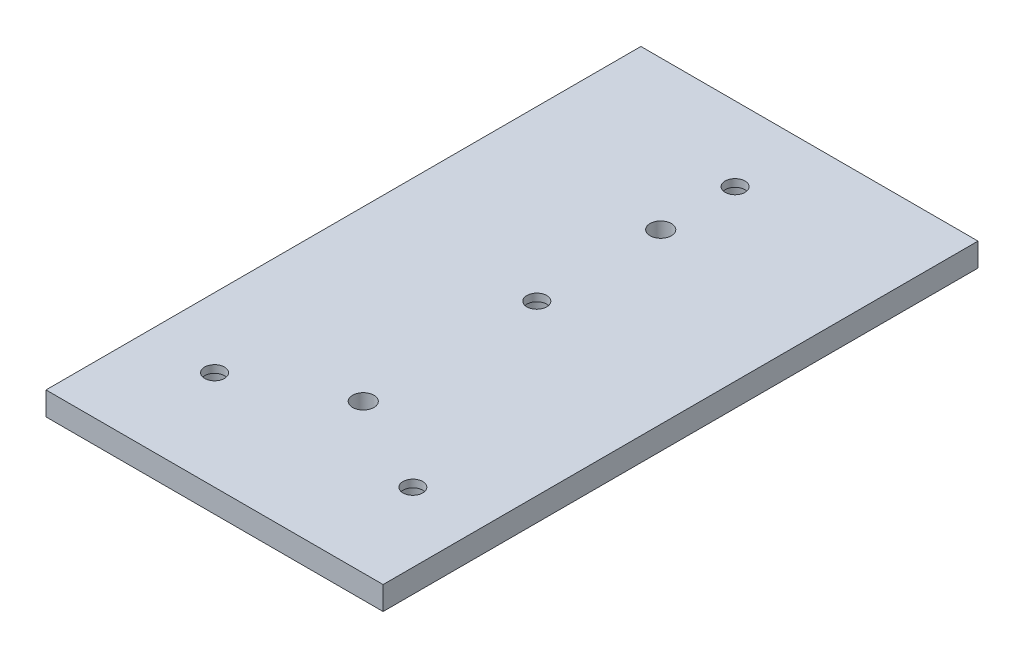
SolidWorks part; units mm, degrees
material "Melamine resin"
ref_plane "Front Plane" through (0, 0, 0) normal (0, 0, 1) x (1, 0, 0)
ref_plane "Top Plane" through (0, 0, 0) normal (0, 1, 0) x (1, 0, 0)
ref_plane "Right Plane" through (0, 0, 0) normal (1, 0, 0) x (0, 0, -1)
sketch "Sketch2" plane through (0, 0, 0) normal (0, 1, 0) x (1, 0, 0)
  line L1 (0, 0) -> (88.9, 0)
  line L2 (0, 0) -> (0, 152.4)
  line L3 (0, 152.4) -> (88.9, 152.4)
  line L10 (88.9, 152.4) -> (88.9, 0)
  dimension "D1" = 152.4
  dimension "D2" = 88.9
extrude "Boss-Extrude1" add sketch "Sketch2" along normal blind 5.9944 contours L3 L10 L1 L2
sketch "Sketch4" plane through (0, 5.9944, 0) normal (0, 1, 0) x (1, 0, 0)
  line L0 (0, 0) -> (0, 152.4) construction
  line L2 (45.72, 114.3) -> (45.72, 38.1) construction
  circle A0 centre (45.72, 114.3) radius 2.7305
  circle A1 centre (45.72, 38.1) radius 2.7305
  point P4 (0, 76.2)
  point P6 (45.72, 76.2)
  dimension "D3" = 5.461
  dimension "D4" = 5.461
  dimension "D1" = 76.2
  dimension "D2" = 45.72
extrude "Cut-Extrude2" cut sketch "Sketch4" against normal through all both
sketch "Sketch7" plane through (0, 5.9944, 0) normal (0, 1, 0) x (1, 0, 0)
  line L0 (0, 0) -> (16.256, 0) construction
  line L1 (0, 152.4) -> (2.54, 152.4)
  line L2 (0, 152.4) -> (0, 0)
  line L3 (0, 0) -> (2.54, 0)
  line L4 (2.54, 152.4) -> (2.54, 0)
  dimension "D1" = 2.54
extrude "Cut-Extrude3" cut sketch "Sketch7" against normal through all both
sketch "Sketch8" plane through (0, 5.9944, 0) normal (0, 1, 0) x (1, 0, 0)
  line L0 (45.72, 133.35) -> (45.72, 82.55) construction
  line L1 (20.32, 25.4) -> (71.12, 25.4) construction
  line L2 (2.54, 0) -> (88.9, 0) construction
  line L3 (2.54, 152.4) -> (88.9, 152.4) construction
  circle A0 centre (20.32, 25.4) radius 2.54
  circle A1 centre (71.12, 25.4) radius 2.54
  circle A2 centre (45.72, 82.55) radius 2.54
  circle A3 centre (45.72, 133.35) radius 2.54
  point P10 (45.72, 0)
  point P11 (45.72, 25.4)
  point P18 (45.72, 152.4)
  point P19 (45.72, 107.95)
  dimension "D1" = 5.08
  dimension "D2" = 5.08
  dimension "D3" = 5.08
  dimension "D4" = 5.08
  dimension "D5" = 50.8
  dimension "D6" = 50.8
  dimension "D7" = 25.4
  dimension "D8" = 19.05
extrude "Cut-Extrude4" cut sketch "Sketch8" against normal through all both and the other way through all
sketch "Sketch9" plane through (0, 0, 0) normal (0, -1, 0) x (1, 0, 0)
  circle A0 centre (20.32, -25.4) radius 3.683
  circle A1 centre (71.12, -25.4) radius 3.683
  circle A2 centre (45.72, -82.55) radius 3.683
  circle A3 centre (45.72, -133.35) radius 3.683
  dimension "D1" = 7.366
  dimension "D2" = 7.366
  dimension "D3" = 7.366
  dimension "D4" = 7.366
extrude "Cut-Extrude5" cut sketch "Sketch9" against normal blind 4.064
equation "\"threaded_insert_hole\"=0.1472"
equation "\"th\"=1.25249"
